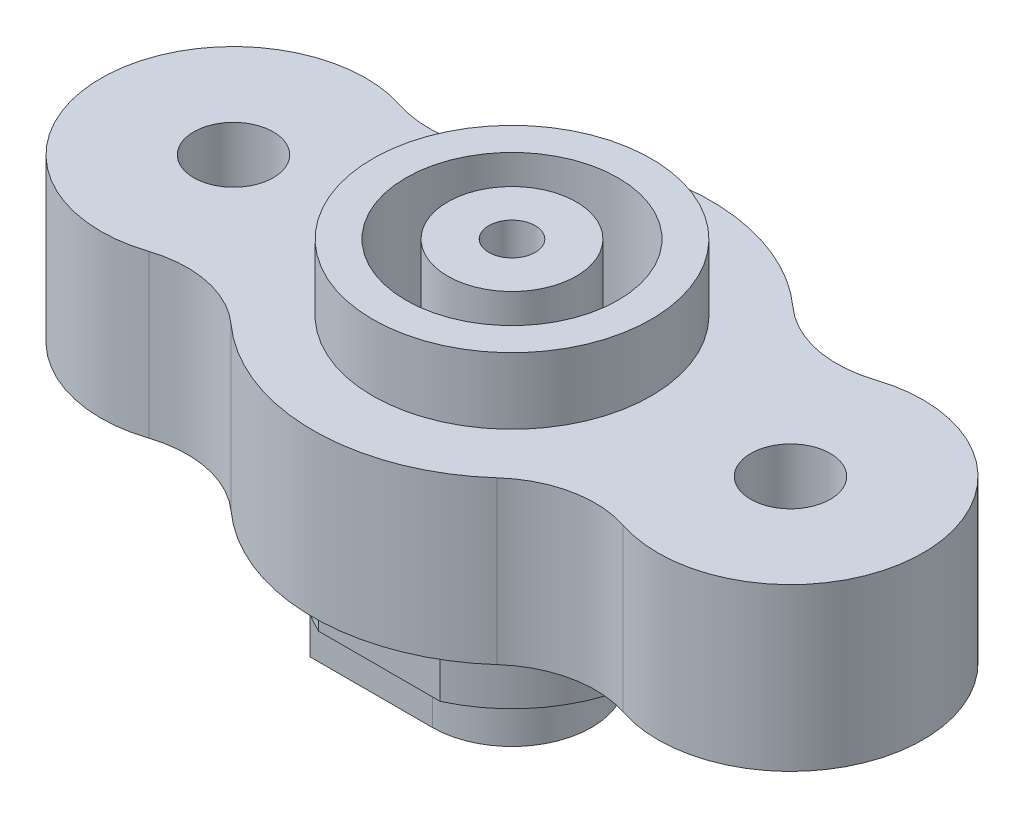
SolidWorks part; units mm, degrees
ref_plane "Front Plane" through (0, 0, 0) normal (0, 0, 1) x (1, 0, 0)
ref_plane "Top Plane" through (0, 0, 0) normal (0, 1, 0) x (1, 0, 0)
ref_plane "Right Plane" through (0, 0, 0) normal (1, 0, 0) x (0, 0, -1)
sketch "Sketch1" plane through (0, 0, 0) normal (0, 1, 0) x (1, 0, 0)
  line L0 (-12.0585, 0) -> (13.5055, 0) construction
  line L1 (0, 34.7285) -> (0, -22.3484) construction
  circle A0 centre (0, 0) radius 7.5
  circle A1 centre (-10.5, 0) radius 5
  circle A2 centre (-10.5, 0) radius 1.5
  circle A3 centre (10.5, 0) radius 5
  circle A4 centre (10.5, 0) radius 1.5
  dimension "D1" = 15
  dimension "D2" = 10
  dimension "D4" = 3
  dimension "D3" = 21
extrude "Boss-Extrude1" add sketch "Sketch1" along normal blind 6.1 contours A0 A1 A2 | A0 A1 | A0 A3 A1 | A3 A0 | A3 A0 A4
sketch "Sketch2" plane through (0, 6.1, 0) normal (0, 1, 0) x (1, 0, 0)
  circle A0 centre (0, 0) radius 5.25
  dimension "D1" = 10.5
extrude "Boss-Extrude2" add sketch "Sketch2" along normal blind 2.5
sketch "Sketch4" plane through (0, 0, 0) normal (0, -1, 0) x (1, 0, 0)
  line L1 (5.5, -5) -> (-5.5, -5)
  line L2 (5.5, -5) -> (5.5, 5)
  line L3 (5.5, 5) -> (-5.5, 5)
  line L4 (-5.5, -5) -> (-5.5, 5)
  line L5 (5.5, -5) -> (-5.5, 5) construction
  line L6 (5.5, 5) -> (-5.5, -5) construction
  circle A0 centre (0, 0) radius 5.5
  point P7 (-6.0756, 3.8172)
  point P10 (0, 0)
  dimension "D1" = 11
  dimension "D2" = 10
extrude "Boss-Extrude3" add sketch "Sketch4" along normal offset from surface (2.85 mm away) 11.45 contours L1 A0 L3 up to face at (0, 8.6, 5.25)
sketch "Sketch3" plane through (0, 8.6, 0) normal (0, 1, 0) x (1, 0, 0)
  circle A0 centre (0, 0) radius 4
  circle A1 centre (0, 0) radius 2.425
  circle A2 centre (0, 0) radius 0.875
  dimension "D1" = 8
  dimension "D2" = 4.85
  dimension "D3" = 1.75
extrude "Cut-Extrude1" cut sketch "Sketch3" against normal blind 8 contours A0 A1 | A2
fillet "Fillet1" radius 4 4 edges at (6.7381, 3.05, -3.2936) (6.7381, 3.05, 3.2936) (-6.7381, 3.05, 3.2936) (-6.7381, 3.05, -3.2936)
sketch "Sketch5" plane through (0, -2.85, 0) normal (0, -1, 0) x (1, 0, 0)
  line L0 (0, 3) -> (-4.6098, 3)
  line L1 (0, -3) -> (-4.6098, -3)
  line L2 (-2.2913, -5) -> (2.2913, -5)
  line L3 (2.2913, 5) -> (-2.2913, 5)
  line L4 (-2.2913, -5) -> (2.2913, -5)
  line L5 (2.2913, 5) -> (-2.2913, 5)
  circle A0 centre (0, 0) radius 3
  arc A3 (2.2913, -5) -> (2.2913, 5) centre (0, 0) ccw
  arc A4 (-2.2913, 5) -> (-2.2913, -5) centre (0, 0) ccw
  arc A5 (2.2913, -5) -> (2.2913, 5) centre (0, 0) ccw
  arc A6 (-2.2913, 5) -> (-2.2913, -5) centre (0, 0) ccw
  arc M9 (-2.2913, 5) -> (-2.2913, -5) centre (0, 0) ccw
  dimension "D1" = 6
  dimension "D2" = 0
extrude "Boss-Extrude4" add sketch "Sketch5" along normal blind 3 contours A0 | A0 L0 L1 M9
